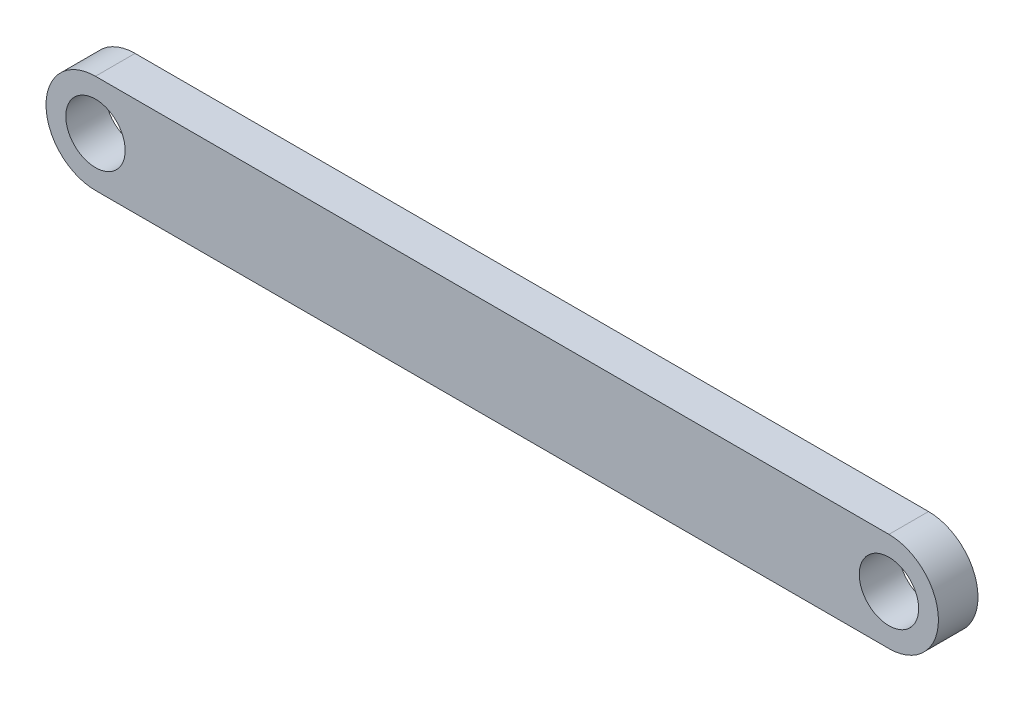
SolidWorks part; units mm, degrees
ref_plane "Front Plane" through (0, 0, 0) normal (0, 0, 1) x (1, 0, 0)
ref_plane "Top Plane" through (0, 0, 0) normal (0, 1, 0) x (1, 0, 0)
ref_plane "Right Plane" through (0, 0, 0) normal (1, 0, 0) x (0, 0, -1)
sketch "Sketch1" plane through (0, 0, 0) normal (0, 0, 1) x (1, 0, 0)
  line L0 (0.1446, -0.0727) -> (40.2446, -0.0727) construction
  line L1 (0.1446, 2.4273) -> (40.2446, 2.4273)
  line L2 (0.1446, -2.5727) -> (40.2446, -2.5727)
  arc A0 (0.1446, 2.4273) -> (0.1446, -2.5727) centre (0.1446, -0.0727) ccw
  arc A1 (40.2446, -2.5727) -> (40.2446, 2.4273) centre (40.2446, -0.0727) ccw
  circle A2 centre (0.1446, -0.0727) radius 1.5
  circle A3 centre (40.2446, -0.0727) radius 1.5
  point P2 (20.1946, -0.0727)
  dimension "D3" = 3
  dimension "D4" = 3
  dimension "D1" = 40.1
  dimension "D2" = 5
extrude "Boss-Extrude1" add sketch "Sketch1" along normal blind 2
